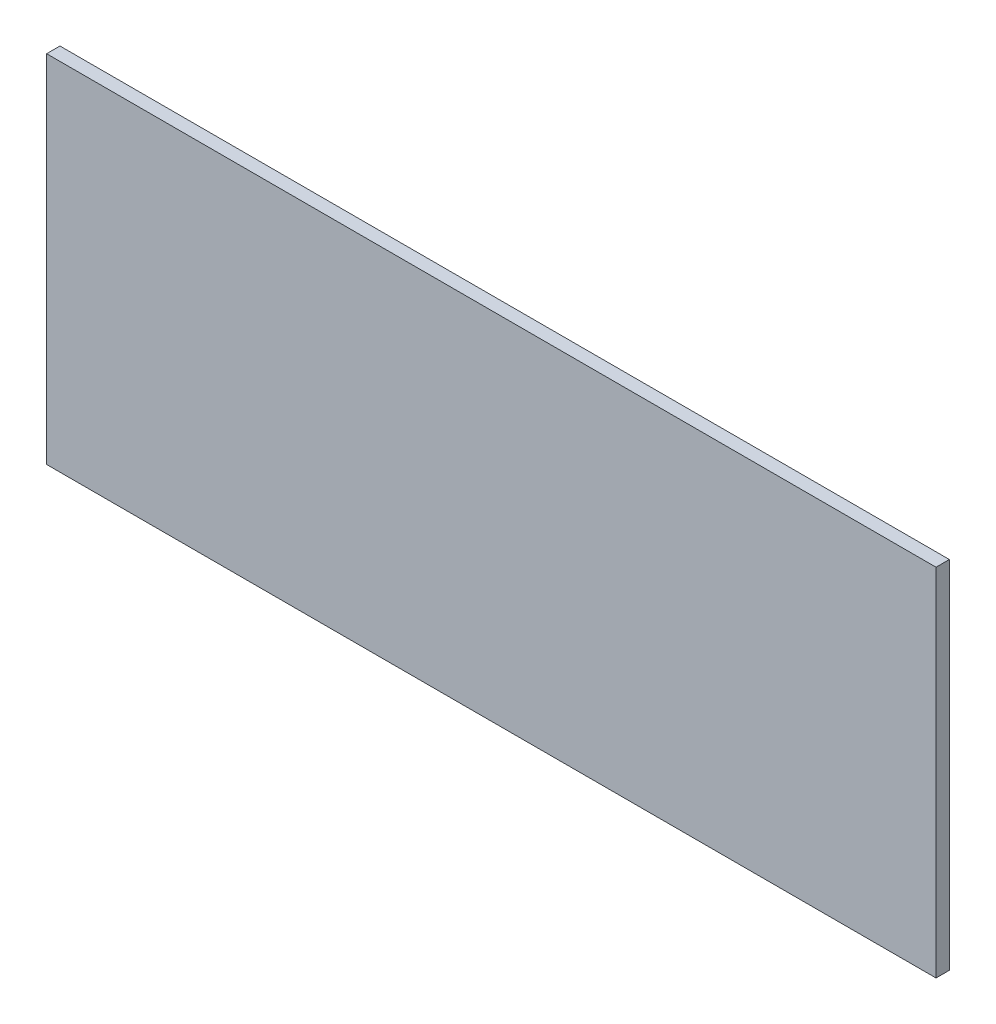
SolidWorks part; units mm, degrees
ref_plane "Front Plane" through (0, 0, 0) normal (0, 0, 1) x (1, 0, 0)
ref_plane "Top Plane" through (0, 0, 0) normal (0, 1, 0) x (1, 0, 0)
ref_plane "Right Plane" through (0, 0, 0) normal (1, 0, 0) x (0, 0, -1)
sketch "Sketch1" plane through (0, 0, 0) normal (0, 0, 1) x (1, 0, 0)
  line L1 (-100, 40) -> (100, 40)
  line L2 (-100, 40) -> (-100, -40)
  line L3 (-100, -40) -> (100, -40)
  line L4 (100, 40) -> (100, -40)
  line L5 (-100, 40) -> (100, -40) construction
  line L6 (-100, -40) -> (100, 40) construction
  point P0 (0, 0)
  dimension "D1" = 200
  dimension "D2" = 80
extrude "Boss-Extrude1" add sketch "Sketch1" along normal blind 3
